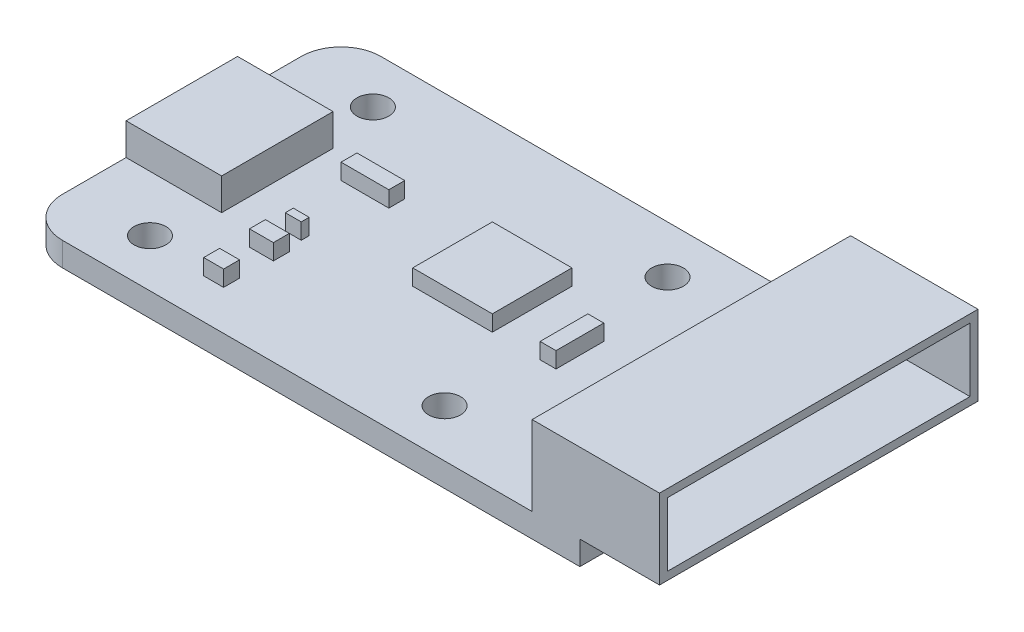
SolidWorks part; units mm, degrees
material "ABS"
ref_plane "Front Plane" through (0, 0, 0) normal (0, 0, 1) x (1, 0, 0)
ref_plane "Top Plane" through (0, 0, 0) normal (0, 1, 0) x (1, 0, 0)
ref_plane "Right Plane" through (0, 0, 0) normal (1, 0, 0) x (0, 0, -1)
sketch "Sketch1" plane through (0, 0, 0) normal (0, 1, 0) x (1, 0, 0)
  line L1 (-17.5, -10) -> (17.5, -10)
  line L2 (-17.5, -10) -> (-17.5, 10)
  line L3 (-17.5, 10) -> (17.5, 10)
  line L4 (17.5, -10) -> (17.5, 10)
  line L5 (-17.5, -10) -> (17.5, 10) construction
  line L6 (-17.5, 10) -> (17.5, -10) construction
  point P0 (0, 0)
  dimension "D1" = 35
  dimension "D2" = 20
extrude "Boss-Extrude1" add sketch "Sketch1" along normal blind 1.5
fillet "Fillet1" radius 2.5 2 edges at (-17.5, 0.75, -10) (-17.5, 0.75, 10)
sketch "Sketch2" plane through (0, 1.5, 0) normal (0, 1, 0) x (1, 0, 0)
  line L0 (-17.5, 0) -> (17.5, 0) construction
  line L1 (-17.5, 7.5) -> (-17.5, -7.5) construction
  line L2 (17.5, -10) -> (17.5, 10) construction
  line L3 (17.5, 10) -> (-15, 10) construction
  circle A0 centre (-12.5, 7) radius 1
  circle A1 centre (6, 7) radius 1
  circle A2 centre (6, -7) radius 1
  circle A3 centre (-12.5, -7) radius 1
  dimension "D1" = 2
  dimension "D2" = 3
  dimension "D3" = 5
  dimension "D4" = 18.5
extrude "Cut-Extrude1" cut sketch "Sketch2" against normal up to surface (1.5 mm away) up to face at (-5.1726, 0, 0)
sketch "Sketch3" plane through (0, 1.5, 0) normal (0, 1, 0) x (1, 0, 0)
  line L0 (-17.5, 7.5) -> (-17.5, -7.5) construction
  line L1 (-11.5, -3.5) -> (-17.5, -3.5)
  line L2 (-11.5, -3.5) -> (-11.5, 3.5)
  line L3 (-11.5, 3.5) -> (-17.5, 3.5)
  line L4 (-17.5, -3.5) -> (-17.5, 3.5)
  line L5 (-11.5, -3.5) -> (-17.5, 3.5) construction
  line L6 (-11.5, 3.5) -> (-17.5, -3.5) construction
  point P0 (-14.5, 0)
  dimension "D1" = 7
  dimension "D2" = 6
  dimension "D3" = 3
extrude "Boss-Extrude2" add sketch "Sketch3" along normal blind 2
sketch "Sketch4" plane through (-17.5, 0, 0) normal (-1, 0, 0) x (0, 0, 1)
  line L1 (-3.25, 3.25) -> (3.25, 3.25)
  line L2 (-3.25, 3.25) -> (-3.25, 1.75)
  line L3 (-3.25, 1.75) -> (3.25, 1.75)
  line L4 (3.25, 3.25) -> (3.25, 1.75)
  line L5 (-3.25, 3.25) -> (3.25, 1.75) construction
  line L6 (-3.25, 1.75) -> (3.25, 3.25) construction
  point P0 (0, 2.5)
  dimension "D1" = 6.5
  dimension "D2" = 1.5
  dimension "D3" = 2.5
extrude "Cut-Extrude2" cut sketch "Sketch4" against normal blind 5.5
sketch "Sketch5" plane through (0, 1.5, 0) normal (0, 1, 0) x (1, 0, 0)
  line L0 (17.5, -10) -> (17.5, 10) construction
  line L1 (14.5, -10) -> (22.5, -10)
  line L2 (14.5, -10) -> (14.5, 10)
  line L3 (14.5, 10) -> (22.5, 10)
  line L4 (22.5, -10) -> (22.5, 10)
  line L5 (14.5, -10) -> (22.5, 10) construction
  line L6 (14.5, 10) -> (22.5, -10) construction
  point P0 (18.5, 0)
  dimension "D1" = 8
  dimension "D2" = 5
  dimension "D3" = 20
extrude "Boss-Extrude3" add sketch "Sketch5" along normal blind 5
sketch "Sketch6" plane through (22.5, 0, 0) normal (1, 0, 0) x (0, 0, -1)
  line L1 (-9.5, 2) -> (9.5, 2)
  line L2 (-9.5, 2) -> (-9.5, 6)
  line L3 (-9.5, 6) -> (9.5, 6)
  line L4 (9.5, 2) -> (9.5, 6)
  line L5 (-9.5, 2) -> (9.5, 6) construction
  line L6 (-9.5, 6) -> (9.5, 2) construction
  point P0 (0, 4)
  dimension "D1" = 4
  dimension "D2" = 4
  dimension "D3" = 19
extrude "Cut-Extrude3" cut sketch "Sketch6" against normal blind 7
sketch "Sketch7" plane through (0, 1.5, 0) normal (0, 1, 0) x (1, 0, 0)
  line L0 (-17.5, 7.5) -> (-17.5, 3.5) construction
  line L1 (-1.5, -1.5) -> (3.5, -1.5)
  line L2 (-1.5, -1.5) -> (-1.5, 3.5)
  line L3 (-1.5, 3.5) -> (3.5, 3.5)
  line L4 (3.5, -1.5) -> (3.5, 3.5)
  line L5 (-1.5, -1.5) -> (3.5, 3.5) construction
  line L6 (-1.5, 3.5) -> (3.5, -1.5) construction
  line L7 (14.5, 10) -> (-15, 10) construction
  point P0 (1, 1)
  dimension "D1" = 5
  dimension "D2" = 5
  dimension "D3" = 18.5
  dimension "D4" = 9
extrude "Boss-Extrude4" add sketch "Sketch7" along normal blind 1
sketch "Sketch8" plane through (0, 1.5, 0) normal (0, 1, 0) x (1, 0, 0)
  line L0 (-15, -10) -> (14.5, -10) construction
  line L1 (-8.625, -7.5) -> (-7.375, -7.5)
  line L2 (-8.625, -7.5) -> (-8.625, -6.5)
  line L3 (-8.625, -6.5) -> (-7.375, -6.5)
  line L4 (-7.375, -7.5) -> (-7.375, -6.5)
  line L5 (-8.625, -7.5) -> (-7.375, -6.5) construction
  line L6 (-8.625, -6.5) -> (-7.375, -7.5) construction
  line L7 (-8.75, -4.5) -> (-7.25, -4.5)
  line L8 (-8.75, -4.5) -> (-8.75, -3.5)
  line L9 (-8.75, -3.5) -> (-7.25, -3.5)
  line L10 (-7.25, -4.5) -> (-7.25, -3.5)
  line L11 (-8.75, -4.5) -> (-7.25, -3.5) construction
  line L12 (-8.75, -3.5) -> (-7.25, -4.5) construction
  line L13 (-8.5, -2.5) -> (-7.5, -2.5)
  line L14 (-8.5, -2.5) -> (-8.5, -2)
  line L15 (-8.5, -2) -> (-7.5, -2)
  line L16 (-7.5, -2.5) -> (-7.5, -2)
  line L17 (-8.5, -2.5) -> (-7.5, -2) construction
  line L18 (-8.5, -2) -> (-7.5, -2.5) construction
  line L19 (-9.5, 2) -> (-6.5, 2)
  line L20 (-9.5, 2) -> (-9.5, 3)
  line L21 (-9.5, 3) -> (-6.5, 3)
  line L22 (-6.5, 2) -> (-6.5, 3)
  line L23 (-9.5, 2) -> (-6.5, 3) construction
  line L24 (-9.5, 3) -> (-6.5, 2) construction
  line L25 (6.5, -1.5) -> (7.5, -1.5)
  line L26 (6.5, -1.5) -> (6.5, 1.5)
  line L27 (6.5, 1.5) -> (7.5, 1.5)
  line L28 (7.5, -1.5) -> (7.5, 1.5)
  line L29 (6.5, -1.5) -> (7.5, 1.5) construction
  line L30 (6.5, 1.5) -> (7.5, -1.5) construction
  line L31 (-17.5, -3.5) -> (-17.5, -7.5) construction
  line L33 (3.5, -1.5) -> (3.5, 3.5) construction
  line L35 (3.5, 3.5) -> (-1.5, 3.5) construction
  point P0 (-8, -7)
  point P5 (-8, -4)
  point P10 (-8, -2.25)
  point P15 (-8, 2.5)
  point P20 (7, 0)
  point P32 (7, 1.5)
  dimension "D1" = 1
  dimension "D2" = 3
  dimension "D3" = 3
  dimension "D4" = 1
  dimension "D5" = 1.25
  dimension "D6" = 1
  dimension "D7" = 1.5
  dimension "D8" = 1
  dimension "D9" = 1
  dimension "D10" = 0.5
  dimension "D11" = 3
  dimension "D12" = 2
  dimension "D13" = 1
  dimension "D14" = 4
  dimension "D15" = 9.5
  dimension "D16" = 3
  dimension "D17" = 2
extrude "Boss-Extrude5" add sketch "Sketch8" along normal blind 1
